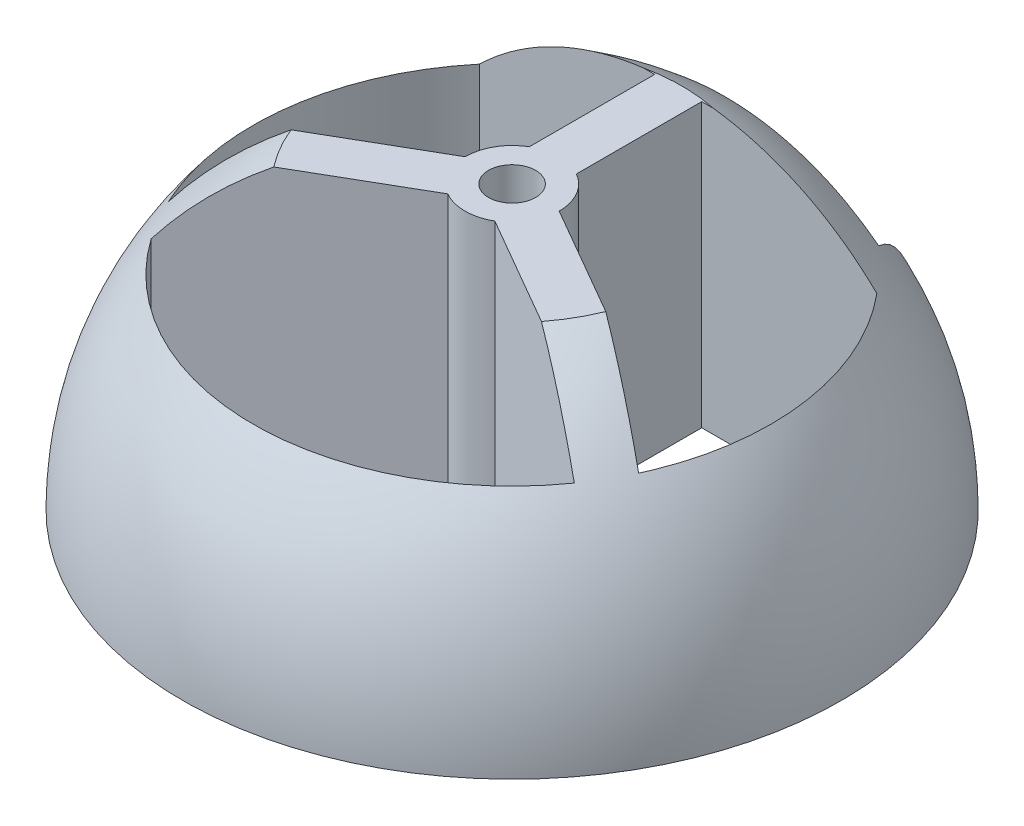
SolidWorks part; units mm, degrees
ref_plane "Front Plane" through (0, 0, 0) normal (0, 0, 1) x (1, 0, 0)
ref_plane "Top Plane" through (0, 0, 0) normal (0, 1, 0) x (1, 0, 0)
ref_plane "Right Plane" through (0, 0, 0) normal (1, 0, 0) x (0, 0, -1)
sketch "Sketch1" plane through (0, 0, 0) normal (0, 0, 1) x (1, 0, 0)
  line L0 (-754.6294, 0) -> (36976.8412, 0) construction
  line L1 (0, -754.6294) -> (0, 36976.8412) construction
  line L2 (0, 14) -> (0, 0)
  line L3 (0, 0) -> (14, 0)
  arc A0 (0, 14) -> (14, 0) centre (0, 0) cw
  dimension "D1" = 14
revolve "Revolve1" add sketch "Sketch1" angle 360 about L1
sketch "Sketch4" plane through (0, 0, 0) normal (0, 1, 0) x (1, 0, 0)
  circle A0 centre (0, 0) radius 11
  circle A1 centre (0, 0) radius 14 construction
  dimension "D1" = 3
extrude "Cut-Extrude4" cut sketch "Sketch4" along normal through all
sketch "Sketch6" plane through (0, 0, 0) normal (0, 1, 0) x (1, 0, 0)
  line L0 (-999.1642, 9.0564) -> (49000.8358, 9.0564) construction
  line L1 (-1006.7099, 13.4164) -> (48993.2901, 13.4164) construction
  line L2 (-6.5172, 9.0564) -> (6.5172, 9.0564)
  line L3 (6.5172, 9.0564) -> (4, 13.4164)
  line L5 (-4, 13.4164) -> (-6.5172, 9.0564)
  line L6 (0, -1000) -> (0, 49000) construction
  arc A0 (-4, 13.4164) -> (4, 13.4164) centre (0, 0) cw
  circle A1 centre (0, 0) radius 14 construction
  dimension "D1" = 4.36
  dimension "D2" = 60
  dimension "D3" = 8
extrude "Cut-Extrude5" cut sketch "Sketch6" along normal through all
sketch "Sketch5" plane through (0, 0, 0) normal (0, 1, 0) x (1, 0, 0)
  line L6 (-1000, 0) -> (49000, 0) construction
  line L7 (-8.4384, 7.0564) -> (-1, 7.0564)
  line L8 (8.4384, 7.0564) -> (1, 7.0564)
  line L9 (-8.4384, 9.0564) -> (-8.4384, 7.0564)
  line L10 (-8.4384, 9.0564) -> (8.4384, 9.0564)
  line L11 (8.4384, 7.0564) -> (8.4384, 9.0564)
  line L12 (-6.2435, 9.0564) -> (-6.5172, 9.0564) construction
  line L14 (0, -1000) -> (0, 49000) construction
  line L15 (-1, 7.0564) -> (-1, 1.7321)
  line L16 (1, 7.0564) -> (1, 1.7321)
  line L17 (-12.5934, -6.1161) -> (-11.5934, -7.8481)
  line L18 (-11.5934, -7.8481) -> (-1, -1.7321)
  line L19 (-12.5934, -6.1161) -> (-2, 0)
  line L20 (1, -1.7321) -> (11.5934, -7.8481)
  line L21 (11.5934, -7.8481) -> (12.5934, -6.1161)
  line L22 (12.5934, -6.1161) -> (2, 0)
  circle A2 centre (0, 0) radius 1
  circle A3 centre (0, 0) radius 11 construction
  circle A5 centre (0, 0) radius 14 construction
  arc A6 (1, 1.7321) -> (2, 0) centre (0, 0) cw
  arc A7 (1, -1.7321) -> (-1, -1.7321) centre (0, 0) cw
  arc A8 (-2, 0) -> (-1, 1.7321) centre (0, 0) cw
  dimension "D3" = 2
  dimension "D4" = 60
  dimension "D2" = 2
  dimension "D1" = 2
  dimension "D5" = 2
  dimension "D6" = 2
extrude "Boss-Extrude1" add sketch "Sketch5" along normal up to surface up to face at (0, 5.9367, -2.9334)
sketch "Sketch7" plane through (0, 0, 0) normal (0, 0, 1) x (1, 0, 0)
  line L0 (-14, 0) -> (14, 0) construction
  line L1 (-9.9793, 12) -> (10.734, 12)
  line L2 (-9.9793, 12) -> (-9.9793, 15.3753)
  line L3 (-9.9793, 15.3753) -> (10.734, 15.3753)
  line L4 (10.734, 12) -> (10.734, 15.3753)
  dimension "D1" = 12
extrude "Cut-Extrude6" cut sketch "Sketch7" against normal through all and the other way through all
